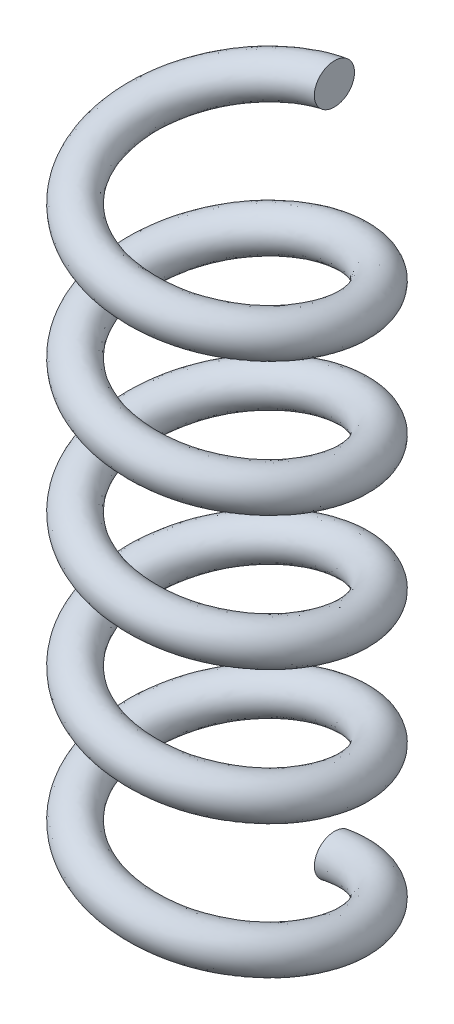
SolidWorks part; units mm, degrees
material "AISI 1020 Steel, Cold Rolled"
ref_plane "Front Plane" through (0, 0, 0) normal (0, 0, 1) x (1, 0, 0)
ref_plane "Top Plane" through (0, 0, 0) normal (0, 1, 0) x (1, 0, 0)
ref_plane "Right Plane" through (0, 0, 0) normal (1, 0, 0) x (0, 0, -1)
sketch "Sketch2" plane through (0, 0, 0) normal (0, 1, 0) x (1, 0, 0)
  circle A0 centre (0, 0) radius 2.0383
curve "Helix/Spiral2" pitch 2.5319 height 12.6594 turns 5
sketch "Sketch4" plane through (0, 0, 0) normal (1, 0, 0) x (0, 0, -1)
  circle A0 centre (2.0384, 12.6595) radius 0.381
sweep "Sweep1" add profiles "Sketch4" path "Helix/Spiral2"
